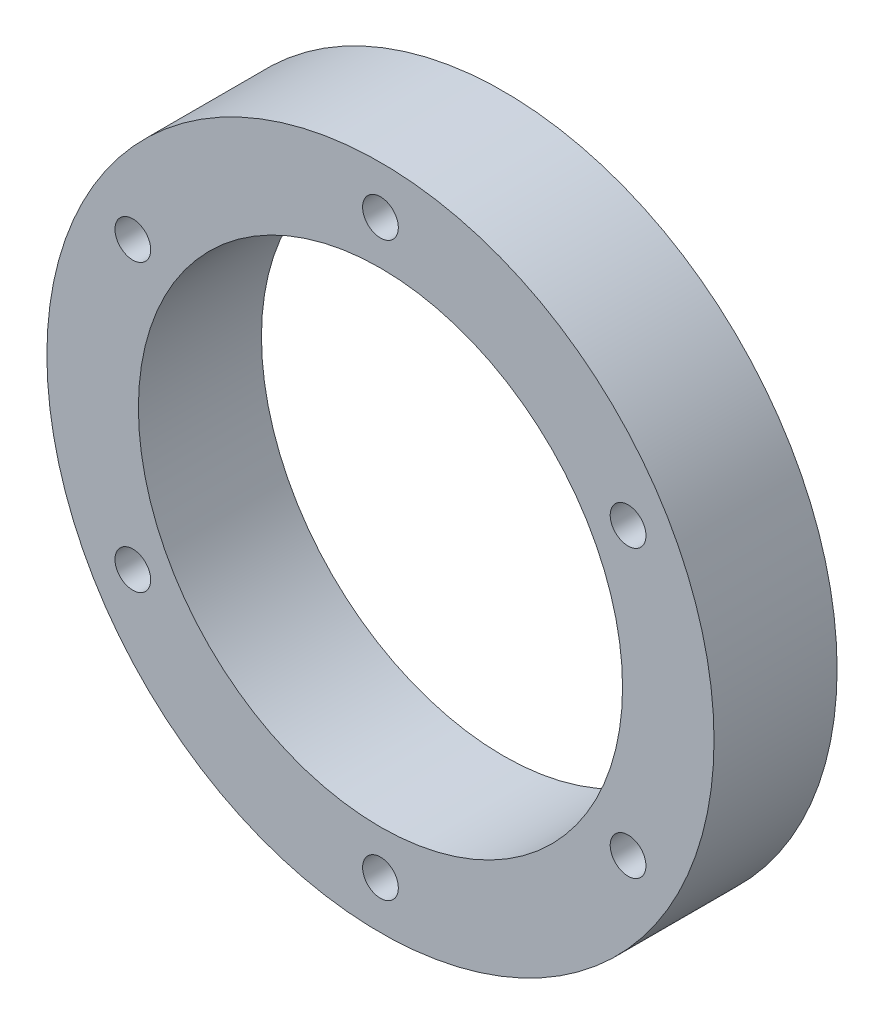
SolidWorks part; units mm, degrees
ref_plane "Front Plane" through (0, 0, 0) normal (0, 0, 1) x (1, 0, 0)
ref_plane "Top Plane" through (0, 0, 0) normal (0, 1, 0) x (1, 0, 0)
ref_plane "Right Plane" through (0, 0, 0) normal (1, 0, 0) x (0, 0, -1)
sketch "Sketch1" plane through (0, 0, 0) normal (0, 0, 1) x (1, 0, 0)
  circle A0 centre (0, 0) radius 16.129
  circle A1 centre (0, 0) radius 22.225
  dimension "D1" = 32.258
  dimension "D2" = 44.45
extrude "Boss-Extrude1" add sketch "Sketch1" along normal blind 8.2
hole_wizard "3/32 (0.09375) Diameter Hole1" positions "Sketch3" profile "Sketch2" hole size "3/32" standard "Ansi Inch"
sketch "Sketch3" plane through (0, 0, 8.2) normal (0, 0, 1) x (1, 0, 0)
  line L0 (0, 0) -> (0, 28.5083) construction
  point P1 (0, 19.05)
  dimension "D1" = 19.05
sketch "Sketch2" plane through (0, 19.05, 8.2) normal (1, 0, 0) x (0, -1, 0)
  line L0 (0, 0) -> (0, 26.1154)
  line L1 (0, 26.1154) -> (1.1906, 25.4)
  line L2 (1.1906, 25.4) -> (1.1906, 0)
  line L5 (1.1906, 0) -> (0, 0)
  line L10 (0, 26.1154) -> (-1.1906, 25.4) construction
  line L11 (0, -6.35) -> (0, 107.95) construction
  dimension "Hole Dia." = 2.3812
  dimension "Hole Depth" = 25.4
  dimension "Drill Angle" = 118
hole_wizard "#2 Clearance Hole1" [suppressed] positions "Sketch7" profile "Sketch6" hole size "#2" standard "Ansi Inch"
sketch "Sketch7" plane through (0, 0, 8.5) normal (0, 0, 1) x (1, 0, 0)
  point P0 (0, -19.05)
  dimension "D1" = 19.05
sketch "Sketch6" plane through (0, -19.05, 8.5) normal (1, 0, 0) x (0, -1, 0)
  line L0 (0, 0) -> (0, 26.0792)
  line L1 (0, 26.0792) -> (1.1303, 25.4)
  line L2 (1.1303, 25.4) -> (1.1303, 0)
  line L5 (1.1303, 0) -> (0, 0)
  line L10 (0, 26.0792) -> (-1.1303, 25.4) construction
  line L11 (0, -6.35) -> (0, 107.95) construction
  dimension "Hole Dia." = 2.2606
  dimension "Hole Depth" = 25.4
  dimension "Drill Angle" = 118
pattern_circular "CirPattern1" count 6 every 60 about axis through (0, 0, 0) along (0, 0, 1) of "3/32 (0.09375) Diameter Hole1"
sketch "Sketch9" [suppressed] plane through (0, 0, 8.5) normal (0, 0, 1) x (1, 0, 0)
  circle A0 centre (-16.4978, 9.525) radius 1.778
